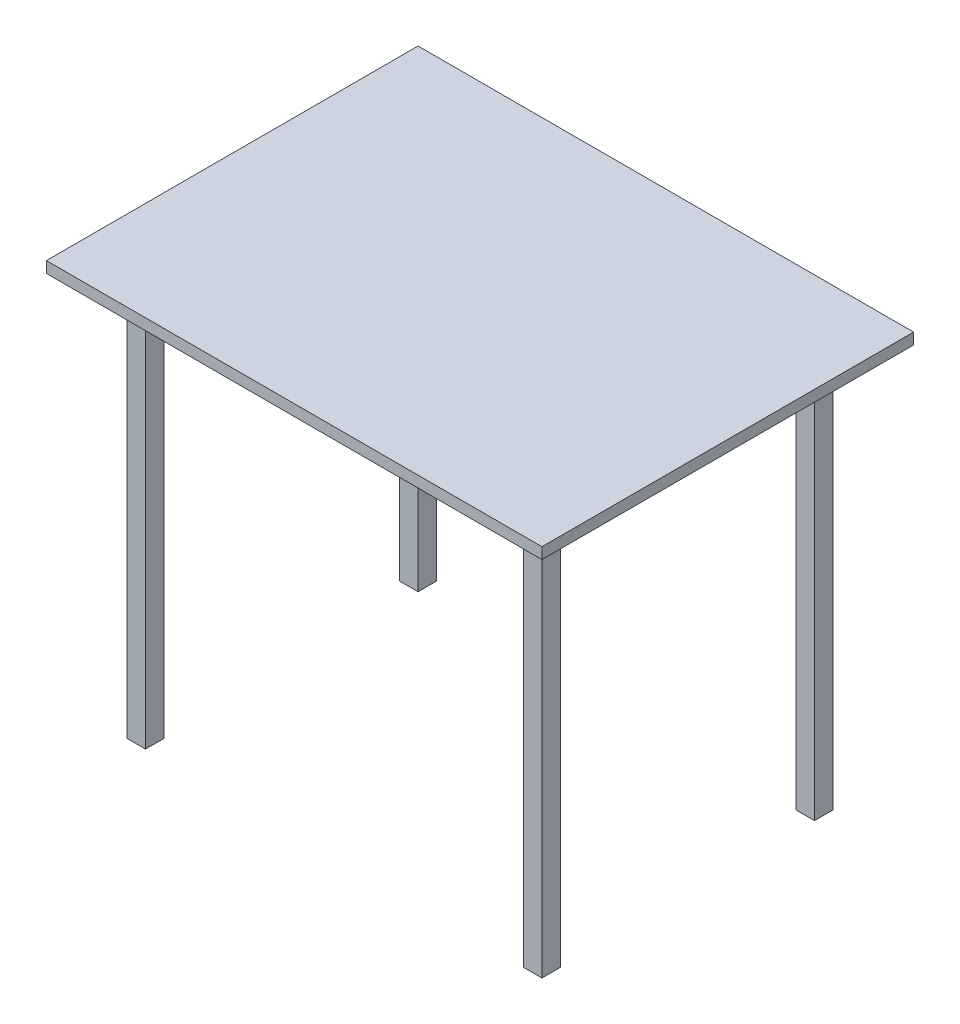
SolidWorks part; units mm, degrees
ref_plane "Спереди" through (0, 0, 0) normal (0, 0, 1) x (1, 0, 0)
ref_plane "Сверху" through (0, 0, 0) normal (0, 1, 0) x (1, 0, 0)
ref_plane "Справа" through (0, 0, 0) normal (1, 0, 0) x (0, 0, -1)
sketch "Эскиз1" plane through (0, 0, 0) normal (0, 1, 0) x (1, 0, 0)
  line L1 (400, -300) -> (-400, -300)
  line L2 (400, -300) -> (400, 300)
  line L3 (400, 300) -> (-400, 300)
  line L4 (-400, -300) -> (-400, 300)
  line L5 (400, -300) -> (-400, 300) construction
  line L6 (400, 300) -> (-400, -300) construction
  point P0 (0, 0)
  dimension "D1" = 800
  dimension "D2" = 600
extrude "Бобышка-Вытянуть1" add sketch "Эскиз1" along normal blind 18
sketch "Эскиз2" plane through (0, 0, 0) normal (0, -1, 0) x (1, 0, 0)
  line L0 (400, -300) -> (-400, -300) construction
  line L1 (320, -220) -> (-320, -220) construction
  line L2 (320, -220) -> (320, 220) construction
  line L3 (320, 220) -> (-320, 220) construction
  line L4 (-320, -220) -> (-320, 220) construction
  line L5 (320, -220) -> (-320, 220) construction
  line L6 (320, 220) -> (-320, -220) construction
  line L7 (-305, 235) -> (-335, 235)
  line L8 (-305, 235) -> (-305, 205)
  line L9 (-305, 205) -> (-335, 205)
  line L10 (-335, 235) -> (-335, 205)
  line L11 (-305, 235) -> (-335, 205) construction
  line L12 (-305, 205) -> (-335, 235) construction
  line L13 (335, 235) -> (305, 235)
  line L14 (335, 235) -> (335, 205)
  line L15 (335, 205) -> (305, 205)
  line L16 (305, 235) -> (305, 205)
  line L17 (335, 235) -> (305, 205) construction
  line L18 (335, 205) -> (305, 235) construction
  line L19 (335, -205) -> (305, -205)
  line L20 (335, -205) -> (335, -235)
  line L21 (335, -235) -> (305, -235)
  line L22 (305, -205) -> (305, -235)
  line L23 (335, -205) -> (305, -235) construction
  line L24 (335, -235) -> (305, -205) construction
  line L25 (-305, -205) -> (-335, -205)
  line L26 (-305, -205) -> (-305, -235)
  line L27 (-305, -235) -> (-335, -235)
  line L28 (-335, -205) -> (-335, -235)
  line L29 (-305, -205) -> (-335, -235) construction
  line L30 (-305, -235) -> (-335, -205) construction
  line L31 (-400, -300) -> (-400, 300) construction
  point P0 (0, 0)
  dimension "D1" = 30
  dimension "D2" = 80
  dimension "D3" = 80
extrude "Бобышка-Вытянуть2" add sketch "Эскиз2" along normal blind 650
